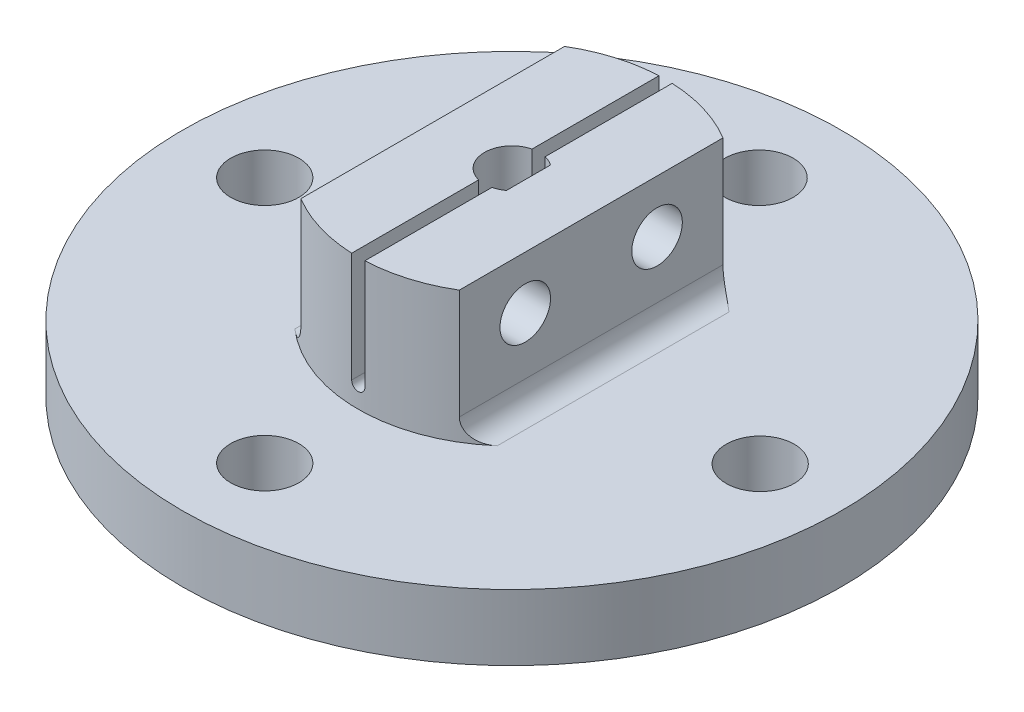
SolidWorks part; units mm, degrees
ref_plane "Front Plane" through (0, 0, 0) normal (0, 0, 1) x (1, 0, 0)
ref_plane "Top Plane" through (0, 0, 0) normal (0, 1, 0) x (1, 0, 0)
ref_plane "Right Plane" through (0, 0, 0) normal (1, 0, 0) x (0, 0, -1)
sketch "Sketch1" plane through (0, 0, 0) normal (0, 1, 0) x (1, 0, 0)
  circle A0 centre (0, 0) radius 19.05
  dimension "D1" = 38.1
extrude "Boss-Extrude1" add sketch "Sketch1" along normal blind 3.81
sketch "Sketch2" plane through (0, 3.81, 0) normal (0, 1, 0) x (1, 0, 0)
  circle A0 centre (0, 0) radius 8.89
  dimension "D1" = 17.78
extrude "Boss-Extrude2" add sketch "Sketch2" along normal blind 7.62
sketch "Sketch3" plane through (0, 11.43, 0) normal (0, 1, 0) x (1, 0, 0)
  line L0 (0.9525, 1.27) -> (0.9525, -1.27)
  circle A0 centre (0, 0) radius 1.5875
  dimension "D1" = 2.54
  dimension "D2" = 3.175
extrude "Cut-Extrude1" cut sketch "Sketch3" against normal through all contours L0 A0
sketch "Sketch4" plane through (0, 0, 0) normal (0, 0, 1) x (1, 0, 0)
  line L0 (-0.381, 11.43) -> (-0.381, 5.08)
  line L1 (0.381, 5.08) -> (0.381, 11.43)
  line L2 (0.381, 11.43) -> (-0.381, 11.43)
  line L3 (8.89, 11.43) -> (-8.89, 11.43) construction
  arc A0 (-0.381, 5.08) -> (0.381, 5.08) centre (0, 5.08) ccw
  point P4 (0, 0)
  point P8 (0, 11.43)
  dimension "D1" = 0.762
  dimension "D2" = 6.35
extrude "Cut-Extrude2" cut sketch "Sketch4" against normal through all both and the other way through all
sketch "Sketch5" plane through (0, 11.43, 0) normal (0, 1, 0) x (1, 0, 0)
  line L0 (-4.5791, 7.62) -> (-4.5791, -7.62)
  line L1 (4.5791, -7.62) -> (4.5791, 7.62)
  arc A0 (-0.381, 8.8818) -> (-0.381, -8.8818) centre (0, 0) ccw construction
  arc A1 (0.381, -8.8818) -> (0.381, 8.8818) centre (0, 0) ccw construction
  arc A2 (-0.381, 8.8818) -> (-0.381, -8.8818) centre (0, 0) ccw
  arc A3 (0.381, -8.8818) -> (0.381, 8.8818) centre (0, 0) ccw
  arc M4 (-0.381, 8.8818) -> (-0.381, -8.8818) centre (0, 0) ccw
  dimension "D1" = 15.24
extrude "Cut-Extrude3" cut sketch "Sketch5" against normal blind 7.62 contours L1 A3 | L0 M4
fillet "Fillet1" radius 1.27 2 edges at (4.5791, 3.81, 0) (-4.5791, 3.81, 0)
sketch "Sketch6" plane through (4.5791, 0, 0) normal (1, 0, 0) x (0, 0, -1)
  line L0 (-3.81, 8.382) -> (3.81, 8.382) construction
  line L1 (19.05, 3.81) -> (-19.05, 3.81) construction
  circle A0 centre (-3.81, 8.382) radius 1.4605
  circle A1 centre (3.81, 8.382) radius 1.4605
  point P4 (0, 8.382)
  dimension "D1" = 2.921
  dimension "D2" = 7.62
  dimension "D3" = 4.572
extrude "Cut-Extrude4" cut sketch "Sketch6" against normal through all
sketch "Sketch7" plane through (0, 3.81, 0) normal (0, 1, 0) x (1, 0, 0)
  circle A0 centre (-14.2875, 0) radius 1.9685
  circle A1 centre (0, 14.2875) radius 1.9685
  circle A2 centre (14.351, 0) radius 1.9685
  circle A3 centre (0, -14.2875) radius 1.9685
  point P8 (0, 0)
  point P10 (0, 0)
  point P11 (0, 0)
  dimension "D1" = 14.2875
  dimension "D5" = 3.937
  dimension "D2" = 14.351
  dimension "D3" = 14.2875
  dimension "D4" = 14.2875
extrude "Cut-Extrude5" cut sketch "Sketch7" against normal through all
